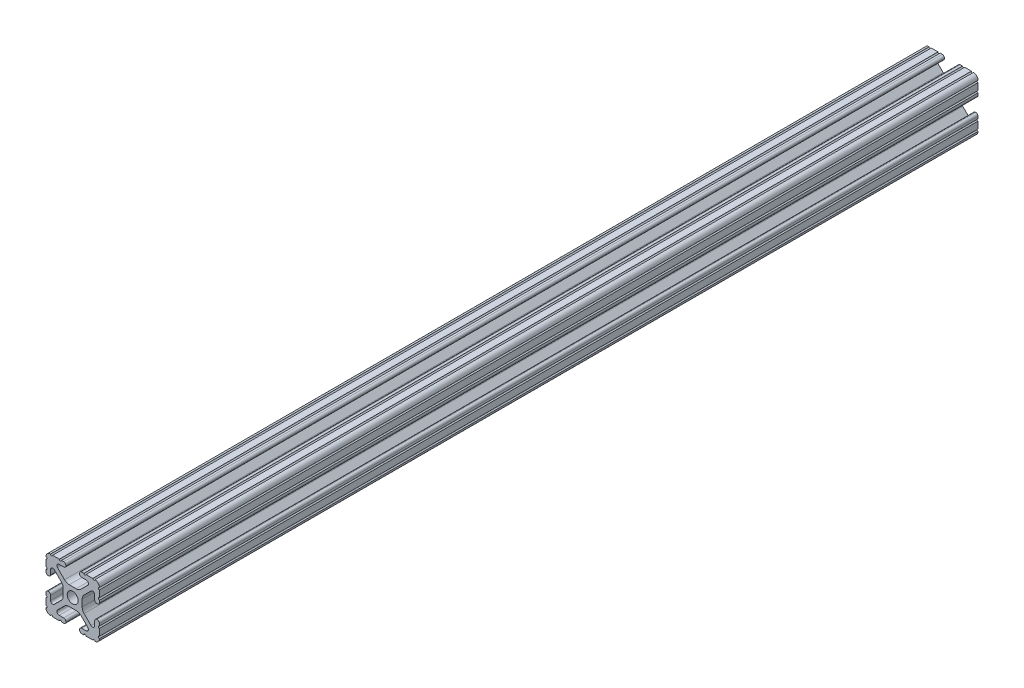
SolidWorks part; units mm, degrees
ref_plane "Front Plane" through (0, 0, 0) normal (0, 0, 1) x (1, 0, 0)
ref_plane "Top Plane" through (0, 0, 0) normal (0, 1, 0) x (1, 0, 0)
ref_plane "Right Plane" through (0, 0, 0) normal (1, 0, 0) x (0, 0, -1)
sketch "Sketch1" plane through (0, 0, 0) normal (0, 0, 1) x (1, 0, 0)
  line L88 (-7.1797, -8.6452) -> (-3.9523, -5.4237)
  line L89 (-1.7093, -4.4958) -> (1.7093, -4.4958)
  line L90 (3.9523, -5.4237) -> (7.1797, -8.6452)
  line L91 (6.4164, -10.4902) -> (4.2875, -10.4902)
  line L92 (3.2385, -11.5392) -> (3.2385, -11.651)
  line L93 (4.2875, -12.7) -> (5.3171, -12.7)
  line L94 (6.3331, -12.7) -> (9.5504, -12.7)
  line L95 (12.7, -9.5504) -> (12.7, -6.3331)
  line L96 (12.7, -5.3171) -> (12.7, -4.2875)
  line L97 (11.651, -3.2385) -> (11.5392, -3.2385)
  line L98 (10.4902, -4.2875) -> (10.4902, -6.4021)
  line L99 (8.7371, -7.1294) -> (5.441, -3.8408)
  line L100 (4.5085, -1.5932) -> (4.5085, 1.5932)
  line L101 (5.441, 3.8408) -> (8.7371, 7.1294)
  line L102 (10.4902, 6.4021) -> (10.4902, 4.2875)
  line L103 (11.5392, 3.2385) -> (11.651, 3.2385)
  line L104 (12.7, 4.2875) -> (12.7, 5.3171)
  line L105 (12.7, 6.3331) -> (12.7, 9.5504)
  line L106 (9.5504, 12.7) -> (6.3331, 12.7)
  line L107 (5.3171, 12.7) -> (4.2875, 12.7)
  line L108 (3.2385, 11.651) -> (3.2385, 11.5392)
  line L109 (4.2875, 10.4902) -> (6.4768, 10.4902)
  line L110 (7.207, 8.7244) -> (3.8983, 5.4232)
  line L111 (1.6558, 4.4958) -> (-1.6558, 4.4958)
  line L112 (-3.8983, 5.4232) -> (-7.207, 8.7244)
  line L113 (-6.4768, 10.4902) -> (-4.2875, 10.4902)
  line L114 (-3.2385, 11.5392) -> (-3.2385, 11.651)
  line L115 (-4.2875, 12.7) -> (-5.3171, 12.7)
  line L116 (-6.3331, 12.7) -> (-9.5504, 12.7)
  line L117 (-12.7, 9.5504) -> (-12.7, 6.3331)
  line L118 (-12.7, 5.3171) -> (-12.7, 4.2875)
  line L119 (-11.651, 3.2385) -> (-11.5392, 3.2385)
  line L120 (-10.4902, 4.2875) -> (-10.4902, 6.4021)
  line L121 (-8.7371, 7.1294) -> (-5.441, 3.8408)
  line L122 (-4.5085, 1.5932) -> (-4.5085, -1.5932)
  line L123 (-5.441, -3.8408) -> (-8.7371, -7.1294)
  line L124 (-10.4902, -6.4021) -> (-10.4902, -4.2875)
  line L125 (-11.5392, -3.2385) -> (-11.651, -3.2385)
  line L126 (-12.7, -4.2875) -> (-12.7, -5.3171)
  line L127 (-12.7, -6.3331) -> (-12.7, -9.5504)
  line L128 (-9.5504, -12.7) -> (-6.3331, -12.7)
  line L129 (-5.3171, -12.7) -> (-4.2875, -12.7)
  line L130 (-3.2385, -11.651) -> (-3.2385, -11.5392)
  line L131 (-4.2875, -10.4902) -> (-6.4164, -10.4902)
  circle A1 centre (0, 0) radius 2.6035
  arc A104 (-7.1797, -8.6452) -> (-6.4164, -10.4902) centre (-6.4164, -9.4098) ccw
  arc A105 (-1.7093, -4.4958) -> (-3.9523, -5.4237) centre (-1.7093, -7.6708) ccw
  arc A106 (3.9523, -5.4237) -> (1.7093, -4.4958) centre (1.7093, -7.6708) ccw
  arc A107 (6.4164, -10.4902) -> (7.1797, -8.6452) centre (6.4164, -9.4098) ccw
  arc A108 (4.2875, -10.4902) -> (3.2385, -11.5392) centre (4.2875, -11.5392) ccw
  arc A109 (3.2385, -11.651) -> (4.2875, -12.7) centre (4.2875, -11.651) ccw
  arc A110 (6.3331, -12.7) -> (5.3171, -12.7) centre (5.8251, -12.7) ccw
  arc A111 (10.5664, -12.6998) -> (9.5504, -12.7) centre (10.0584, -12.7) ccw
  arc A112 (10.5664, -12.6998) -> (12.6998, -10.5664) centre (10.5918, -10.5918) ccw
  arc A113 (12.7, -9.5504) -> (12.6998, -10.5664) centre (12.7, -10.0584) ccw
  arc A114 (12.7, -5.3171) -> (12.7, -6.3331) centre (12.7, -5.8251) ccw
  arc A115 (12.7, -4.2875) -> (11.651, -3.2385) centre (11.651, -4.2875) ccw
  arc A116 (11.5392, -3.2385) -> (10.4902, -4.2875) centre (11.5392, -4.2875) ccw
  arc A117 (8.7371, -7.1294) -> (10.4902, -6.4021) centre (9.4628, -6.4021) ccw
  arc A118 (4.5085, -1.5932) -> (5.441, -3.8408) centre (7.6835, -1.5932) ccw
  arc A119 (5.441, 3.8408) -> (4.5085, 1.5932) centre (7.6835, 1.5932) ccw
  arc A120 (10.4902, 6.4021) -> (8.7371, 7.1294) centre (9.4628, 6.4021) ccw
  arc A121 (10.4902, 4.2875) -> (11.5392, 3.2385) centre (11.5392, 4.2875) ccw
  arc A122 (11.651, 3.2385) -> (12.7, 4.2875) centre (11.651, 4.2875) ccw
  arc A123 (12.7, 6.3331) -> (12.7, 5.3171) centre (12.7, 5.8251) ccw
  arc A124 (12.6998, 10.5664) -> (12.7, 9.5504) centre (12.7, 10.0584) ccw
  arc A125 (12.6998, 10.5664) -> (10.5664, 12.6998) centre (10.5918, 10.5918) ccw
  arc A126 (9.5504, 12.7) -> (10.5664, 12.6998) centre (10.0584, 12.7) ccw
  arc A127 (5.3171, 12.7) -> (6.3331, 12.7) centre (5.8251, 12.7) ccw
  arc A128 (4.2875, 12.7) -> (3.2385, 11.651) centre (4.2875, 11.651) ccw
  arc A129 (3.2385, 11.5392) -> (4.2875, 10.4902) centre (4.2875, 11.5392) ccw
  arc A130 (7.207, 8.7244) -> (6.4768, 10.4902) centre (6.4768, 9.4563) ccw
  arc A131 (1.6558, 4.4958) -> (3.8983, 5.4232) centre (1.6558, 7.6708) ccw
  arc A132 (-3.8983, 5.4232) -> (-1.6558, 4.4958) centre (-1.6558, 7.6708) ccw
  arc A133 (-6.4768, 10.4902) -> (-7.207, 8.7244) centre (-6.4768, 9.4563) ccw
  arc A134 (-4.2875, 10.4902) -> (-3.2385, 11.5392) centre (-4.2875, 11.5392) ccw
  arc A135 (-3.2385, 11.651) -> (-4.2875, 12.7) centre (-4.2875, 11.651) ccw
  arc A136 (-6.3331, 12.7) -> (-5.3171, 12.7) centre (-5.8251, 12.7) ccw
  arc A137 (-10.5664, 12.6998) -> (-9.5504, 12.7) centre (-10.0584, 12.7) ccw
  arc A138 (-10.5664, 12.6998) -> (-12.6998, 10.5664) centre (-10.5918, 10.5918) ccw
  arc A139 (-12.7, 9.5504) -> (-12.6998, 10.5664) centre (-12.7, 10.0584) ccw
  arc A140 (-12.7, 5.3171) -> (-12.7, 6.3331) centre (-12.7, 5.8251) ccw
  arc A141 (-12.7, 4.2875) -> (-11.651, 3.2385) centre (-11.651, 4.2875) ccw
  arc A142 (-11.5392, 3.2385) -> (-10.4902, 4.2875) centre (-11.5392, 4.2875) ccw
  arc A143 (-8.7371, 7.1294) -> (-10.4902, 6.4021) centre (-9.4628, 6.4021) ccw
  arc A144 (-4.5085, 1.5932) -> (-5.441, 3.8408) centre (-7.6835, 1.5932) ccw
  arc A145 (-5.441, -3.8408) -> (-4.5085, -1.5932) centre (-7.6835, -1.5932) ccw
  arc A146 (-10.4902, -6.4021) -> (-8.7371, -7.1294) centre (-9.4628, -6.4021) ccw
  arc A147 (-10.4902, -4.2875) -> (-11.5392, -3.2385) centre (-11.5392, -4.2875) ccw
  arc A148 (-11.651, -3.2385) -> (-12.7, -4.2875) centre (-11.651, -4.2875) ccw
  arc A149 (-12.7, -6.3331) -> (-12.7, -5.3171) centre (-12.7, -5.8251) ccw
  arc A150 (-12.6998, -10.5664) -> (-12.7, -9.5504) centre (-12.7, -10.0584) ccw
  arc A151 (-12.6998, -10.5664) -> (-10.5664, -12.6998) centre (-10.5918, -10.5918) ccw
  arc A152 (-9.5504, -12.7) -> (-10.5664, -12.6998) centre (-10.0584, -12.7) ccw
  arc A153 (-5.3171, -12.7) -> (-6.3331, -12.7) centre (-5.8251, -12.7) ccw
  arc A154 (-4.2875, -12.7) -> (-3.2385, -11.651) centre (-4.2875, -11.651) ccw
  arc A155 (-3.2385, -11.5392) -> (-4.2875, -10.4902) centre (-4.2875, -11.5392) ccw
extrude "Boss-Extrude1" add sketch "Sketch1" along normal mid plane 609.6
sketch "Sketch2" plane through (12.7, 0, 0) normal (1, 0, 0) x (0, 0, -1)
  line L1 (128.9267, -14.2345) -> (310.7431, -14.2345)
  line L2 (310.7431, -14.2345) -> (310.7431, 13.9053)
  line L3 (310.7431, 13.9053) -> (128.9267, 13.9053)
  line L8 (128.9267, -14.2345) -> (128.9267, 13.9053)
  line L9 (-305.4758, 13.3523) -> (-289.2182, 13.3523)
  line L10 (-305.4758, 13.3523) -> (-305.4758, -14.2345)
  line L11 (-305.4758, -14.2345) -> (-289.2182, -14.2345)
  line L12 (-289.2182, 13.3523) -> (-289.2182, -14.2345)
  point P0 (128.9267, 13.9053)
extrude "Cut-Extrude1" cut sketch "Sketch2" against normal blind 26.162 and the other way blind 1.778
